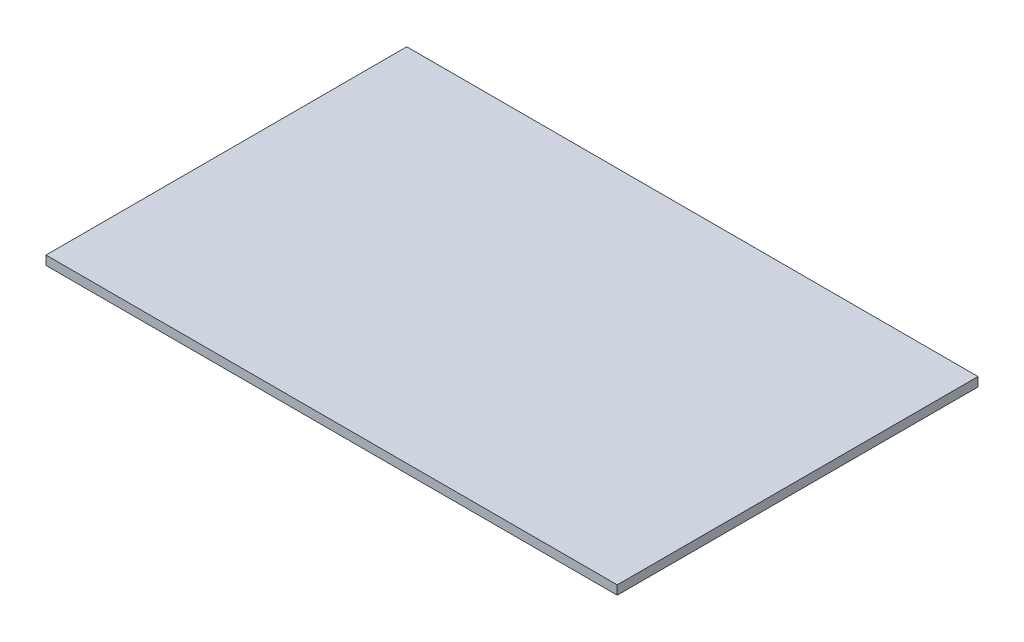
SolidWorks part; units mm, degrees
ref_plane "Front Plane" through (0, 0, 0) normal (0, 0, 1) x (1, 0, 0)
ref_plane "Top Plane" through (0, 0, 0) normal (0, 1, 0) x (1, 0, 0)
ref_plane "Right Plane" through (0, 0, 0) normal (1, 0, 0) x (0, 0, -1)
sketch "Sketch1" plane through (0, 0, 0) normal (0, 1, 0) x (1, 0, 0)
  line L1 (0, 0) -> (190, 0)
  line L2 (0, 0) -> (0, 120)
  line L3 (0, 120) -> (190, 120)
  line L4 (190, 0) -> (190, 120)
  dimension "D1" = 190
  dimension "D2" = 120
extrude "Boss-Extrude1" add sketch "Sketch1" along normal blind 3
